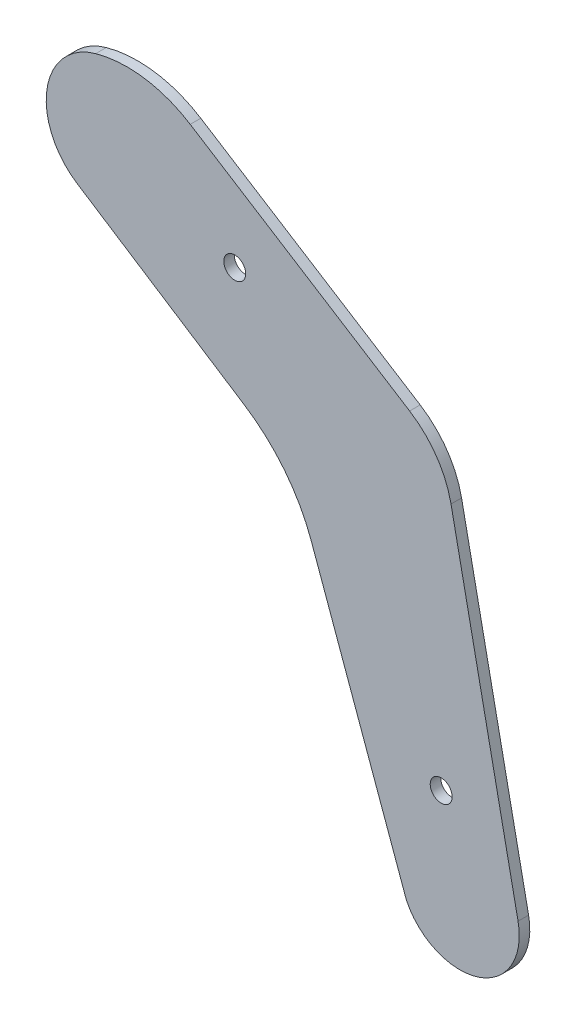
SolidWorks part; units mm, degrees
ref_plane "Front Plane" through (0, 0, 0) normal (0, 0, 1) x (1, 0, 0)
ref_plane "Top Plane" through (0, 0, 0) normal (0, 1, 0) x (1, 0, 0)
ref_plane "Right Plane" through (0, 0, 0) normal (1, 0, 0) x (0, 0, -1)
ref_plane "Plane1" through (0, 0, 0) normal (0, 0, -1) x (-1, 0, 0)
sketch "Sketch1" plane through (0, 0, 0) normal (0, 0, -1) x (-1, 0, 0)
  line L3 (165.7851, 142.9468) -> (130.9909, 174.5742)
  line L4 (130.9909, 174.5742) -> (31.9811, 112.057)
  line L23 (77.485, 85.8604) -> (165.7851, 142.9468)
  line L25 (31.9811, 112.057) -> (9.4092, 1.7104)
  line L29 (77.485, 85.8604) -> (43.0106, -9.6413)
  arc A4 (9.4092, 1.7104) -> (43.0106, -9.6413) centre (26.9175, -1.871) ccw
  circle A5 centre (32.554, 24.2134) radius 3.302
  circle A6 centre (94.7071, 129.4769) radius 3.302
  dimension "D3" = 6.604
  dimension "D4" = 6.604
extrude "Boss-Extrude1" add sketch "Sketch1" against normal blind 3.175
fillet "Fillet6" radius 35.56 1 edges at (-130.9909, 174.5742, 1.5875)
fillet "Fillet10" radius 27.94 1 edges at (-31.9811, 112.057, 1.5875)
fillet "Fillet13" radius 50.8 1 edges at (-77.485, 85.8604, 1.5875)
fillet "Fillet16" radius 20.32 1 edges at (-165.7851, 142.9468, 1.5875)
